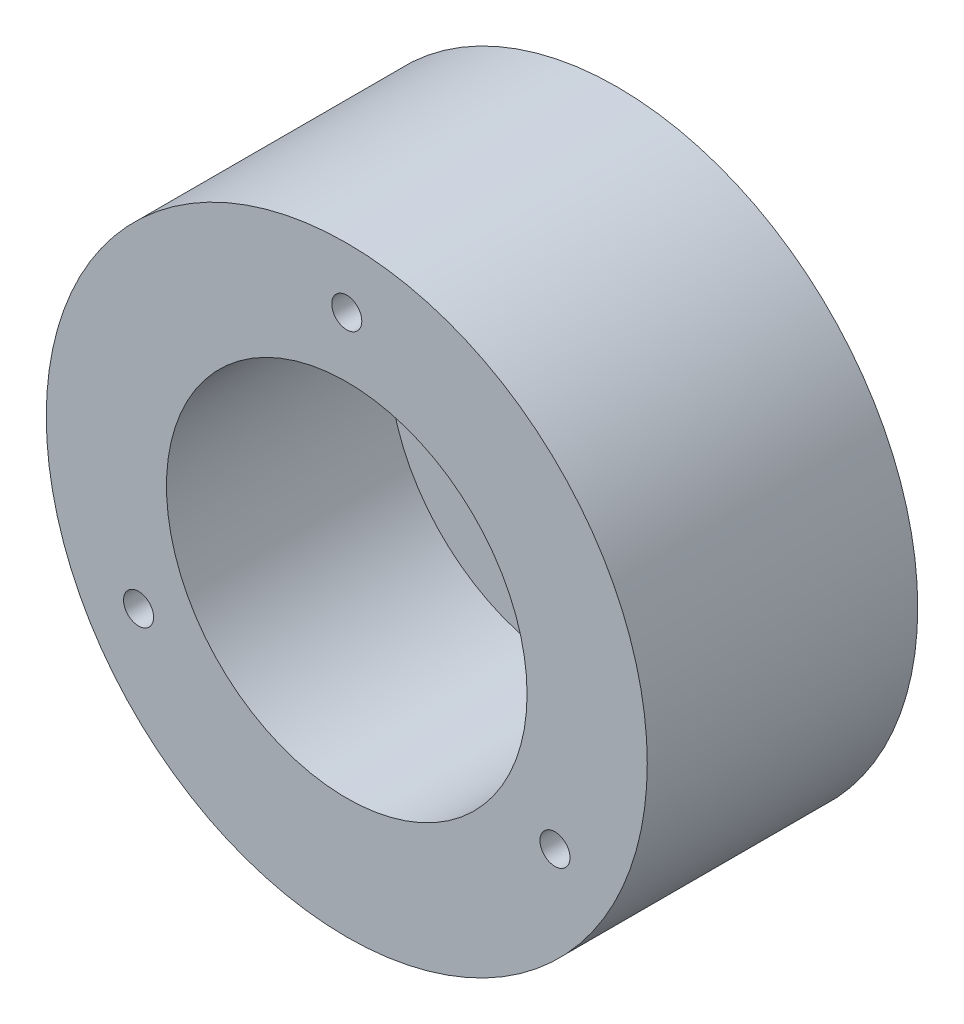
SolidWorks part; units mm, degrees
ref_plane "Front Plane" through (0, 0, 0) normal (0, 0, 1) x (1, 0, 0)
ref_plane "Top Plane" through (0, 0, 0) normal (0, 1, 0) x (1, 0, 0)
ref_plane "Right Plane" through (0, 0, 0) normal (1, 0, 0) x (0, 0, -1)
sketch "Sketch1" plane through (0, 0, 0) normal (0, 0, 1) x (1, 0, 0)
  circle A0 centre (0, 0) radius 50
  circle A1 centre (0, 0) radius 16
  dimension "D1" = 100
extrude "Boss-Extrude1" add sketch "Sketch1" along normal blind 8
sketch "Sketch2" plane through (0, 0, 8) normal (0, 0, 1) x (1, 0, 0)
  circle A0 centre (0, 0) radius 50
  circle A1 centre (0, 0) radius 30
  dimension "D1" = 20
  dimension "D2" = 100
extrude "Boss-Extrude2" add sketch "Sketch2" along normal up to surface (37 mm away)
sketch "Sketch3" plane through (0, 0, 45) normal (0, 0, 1) x (1, 0, 0)
  circle A0 centre (0, 40) radius 2.5
  circle A1 centre (34.641, -20) radius 2.5
  circle A2 centre (-34.641, -20) radius 2.5
extrude "Cut-Extrude1" cut sketch "Sketch3" against normal through all
sketch "Sketch4" plane through (0, 0, 8) normal (0, 0, 1) x (1, 0, 0)
  circle A0 centre (0, 20) radius 2.5
  circle A1 centre (20, 0) radius 2.5
  circle A2 centre (0, -20) radius 2.5
  circle A3 centre (-20, 0) radius 2.5
  dimension "D1" = 5
  dimension "D2" = 4
extrude "Cut-Extrude2" cut sketch "Sketch4" against normal through all
